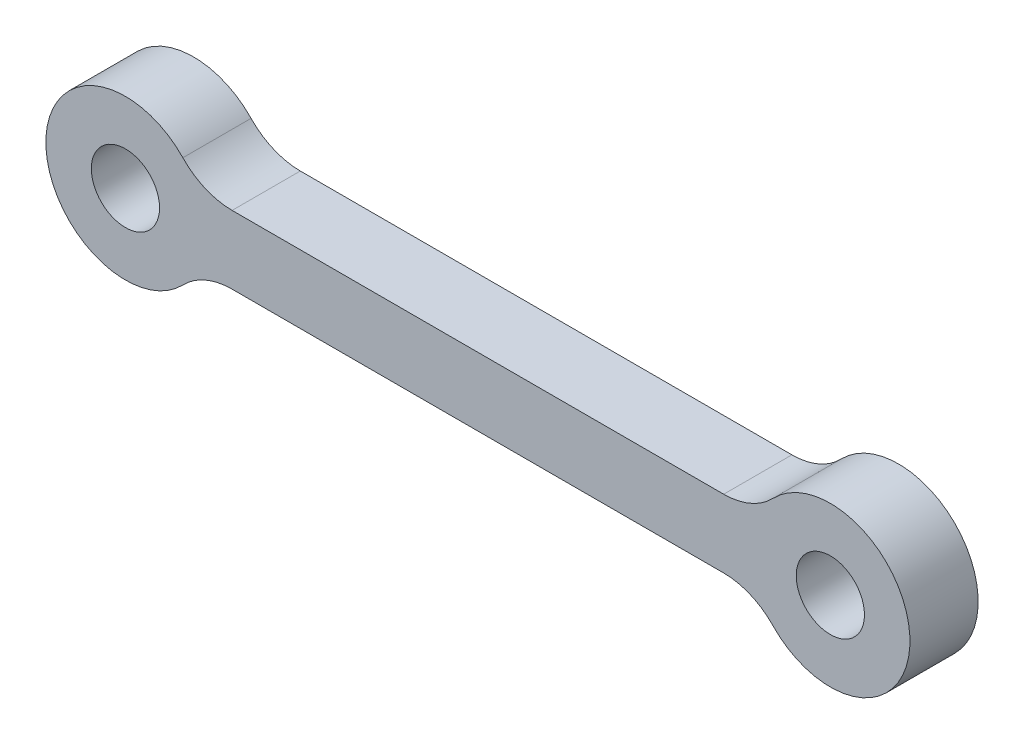
SolidWorks part; units mm, degrees
ref_plane "Front Plane" through (0, 0, 0) normal (0, 0, 1) x (1, 0, 0)
ref_plane "Top Plane" through (0, 0, 0) normal (0, 1, 0) x (1, 0, 0)
ref_plane "Right Plane" through (0, 0, 0) normal (1, 0, 0) x (0, 0, -1)
sketch "Sketch1" plane through (0, 0, 0) normal (0, 0, 1) x (1, 0, 0)
  line L1 (-12.3377, 1.5) -> (12.3377, 1.5)
  line L3 (-12.3377, -1.5) -> (12.3377, -1.5)
  line L5 (-15.5, 1.5) -> (15.5, -1.5) construction
  line L6 (-15.5, -1.5) -> (15.5, 1.5) construction
  circle A0 centre (-15.5, 0) radius 1.5
  circle A1 centre (-15.5, 0) radius 3.5
  circle A2 centre (15.5, 0) radius 1.5
  circle A3 centre (15.5, 0) radius 3.5
  point P0 (0, 0)
  dimension "D2" = 7
  dimension "D3" = 3
  dimension "D4" = 3
  dimension "D5" = 7
  dimension "D1" = 31
extrude "Boss-Extrude1" add sketch "Sketch1" along normal mid plane 3 contours A1 A0 | A3 L1 A1 L3 | A3 A2
fillet "Fillet1" radius 3 4 edges at (12.3377, -1.5, 0) (12.3377, 1.5, 0) (-12.3377, 1.5, 0) (-12.3377, -1.5, 0)
